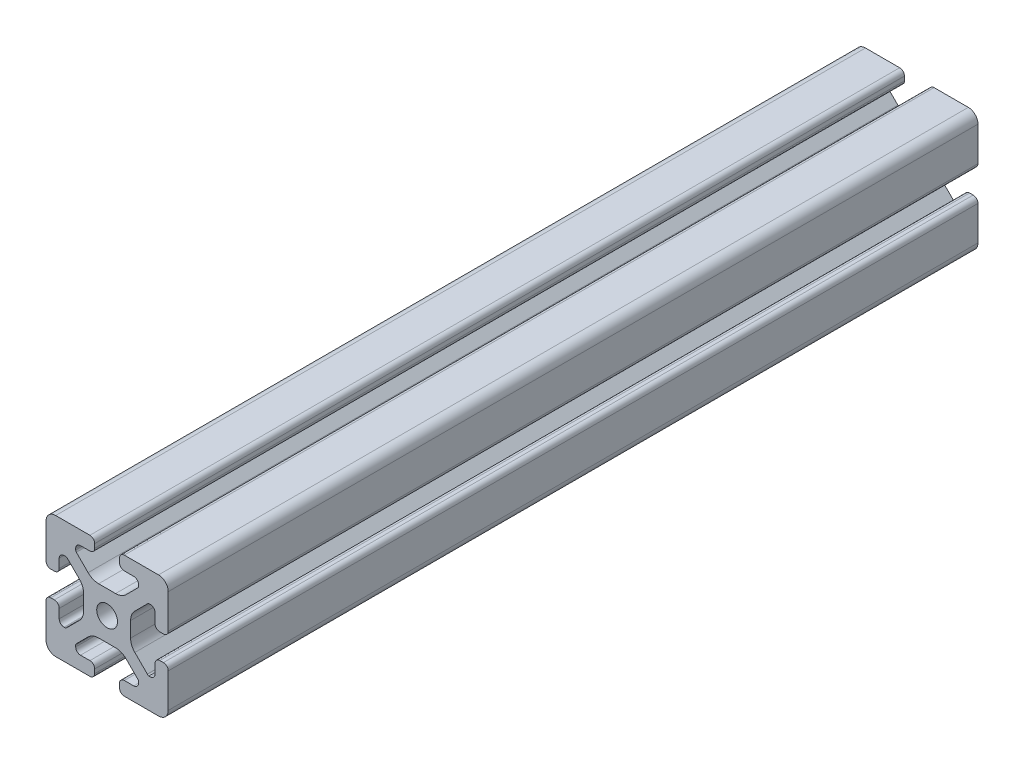
SolidWorks part; units mm, degrees
material "6105-T5 Aluminum"
ref_plane "Front Plane" through (0, 0, 0) normal (0, 0, 1) x (1, 0, 0)
ref_plane "Top Plane" through (0, 0, 0) normal (0, 1, 0) x (1, 0, 0)
ref_plane "Right Plane" through (0, 0, 0) normal (1, 0, 0) x (0, 0, -1)
sketch "Sketch1" plane through (0, 0, 0) normal (0, 0, 1) x (1, 0, 0)
  line L0 (0, 19.7407) -> (0, -19.7407) construction
  line L1 (19.0335, 0) -> (-20.7246, 0) construction
  line L2 (-8.715, -15.5246) -> (-5.63, -15.5246)
  line L3 (-10.285, -13.9546) -> (-10.285, -13.4925)
  line L4 (-6.2171, -9.1098) -> (-10.0624, -12.9551)
  line L5 (2.7773, -7.685) -> (-2.7773, -7.685)
  line L6 (10.0624, -12.9551) -> (6.2171, -9.1098)
  line L7 (10.285, -13.9546) -> (10.285, -13.4925)
  line L8 (5.63, -15.5246) -> (8.715, -15.5246)
  line L9 (4.06, -18.43) -> (4.06, -17.0946)
  line L10 (-4.06, -18.43) -> (-4.06, -17.0946)
  line L11 (15.68, -8.7154) -> (15.68, -5.63)
  line L12 (-14.11, -10.2854) -> (-13.8169, -10.2854)
  line L13 (20, -16.83) -> (20, -5.63)
  line L14 (20, 5.63) -> (20, 13.0011)
  line L15 (-16.83, 20) -> (-5.63, 20)
  line L16 (5.63, 20) -> (12.9796, 20)
  line L18 (-8.715, 15.5246) -> (-5.63, 15.5246)
  line L19 (-20, -17.0184) -> (-20, -5.7579)
  line L20 (-20, 5.573) -> (-20, 13.0045)
  line L21 (-15.68, -8.7154) -> (-15.68, -5.7579)
  line L23 (-16.6746, -20) -> (-5.63, -20)
  line L24 (5.63, -20) -> (13, -20)
  line L53 (14.11, -10.2854) -> (13.6201, -10.2854)
  line L54 (13.1637, -9.947) -> (9.0762, -5.8595)
  line L55 (7.685, -2.5008) -> (7.685, 2.5008)
  line L56 (9.0762, 5.8595) -> (13.2795, 10.0628)
  line L57 (13.8169, 10.2854) -> (14.11, 10.2854)
  line L58 (15.68, 8.7154) -> (15.68, 5.63)
  line L59 (17.25, 4.06) -> (18.43, 4.06)
  line L61 (20, 13.0011) -> (20, 16.83)
  line L62 (16.83, 20) -> (12.9796, 20)
  line L64 (4.06, 18.43) -> (4.06, 17.0946)
  line L65 (5.63, 15.5246) -> (8.715, 15.5246)
  line L66 (10.285, 13.9546) -> (10.285, 13.4925)
  line L67 (10.0624, 12.9551) -> (6.2171, 9.1098)
  line L68 (2.7773, 7.685) -> (-2.7773, 7.685)
  line L69 (-6.2171, 9.1098) -> (-10.0624, 12.9551)
  line L70 (-10.285, 13.4925) -> (-10.285, 13.9546)
  line L72 (-4.06, 17.0946) -> (-4.06, 18.43)
  line L75 (-20, 16.83) -> (-20, 13.0045)
  line L77 (-18.43, 4.003) -> (-17.25, 4.003)
  line L78 (-15.68, 5.573) -> (-15.68, 8.4757)
  line L79 (-14.0552, 10.0447) -> (-13.7199, 10.033)
  line L80 (-13.0405, 9.8238) -> (-9.0762, 5.8595)
  line L81 (-7.685, 2.5008) -> (-7.685, -2.5008)
  line L82 (-9.0762, -5.8595) -> (-13.2795, -10.0628)
  line L85 (-17.25, -4.1204) -> (-18.43, -4.1204)
  line L100 (13, -20) -> (16.83, -20)
  line L103 (18.43, -4.06) -> (17.25, -4.06)
  arc A0 (-5.63, -15.5246) -> (-4.06, -17.0946) centre (-5.63, -17.0946) cw
  arc A1 (-8.715, -15.5246) -> (-10.285, -13.9546) centre (-8.715, -13.9546) cw
  arc A2 (-10.285, -13.4925) -> (-10.0624, -12.9551) centre (-9.525, -13.4925) cw
  arc A3 (-6.2171, -9.1098) -> (-2.7773, -7.685) centre (-2.7773, -12.5496) cw
  arc A4 (2.7773, -7.685) -> (6.2171, -9.1098) centre (2.7773, -12.5496) cw
  arc A5 (10.0624, -12.9551) -> (10.285, -13.4925) centre (9.525, -13.4925) cw
  arc A6 (10.285, -13.9546) -> (8.715, -15.5246) centre (8.715, -13.9546) cw
  arc A7 (4.06, -17.0946) -> (5.63, -15.5246) centre (5.63, -17.0946) cw
  arc A8 (5.63, -20) -> (4.06, -18.43) centre (5.63, -18.43) cw
  arc A9 (-4.06, -18.43) -> (-5.63, -20) centre (-5.63, -18.43) cw
  circle A45 centre (0, 0) radius 3.4
  arc A46 (17.25, -4.06) -> (15.68, -5.63) centre (17.25, -5.63) ccw
  arc A47 (14.11, -10.2854) -> (15.68, -8.7154) centre (14.11, -8.7154) ccw
  arc A48 (13.1637, -9.947) -> (13.6201, -10.2854) centre (13.8117, -9.55) ccw
  arc A49 (7.685, -2.5008) -> (9.0762, -5.8595) centre (12.435, -2.5008) ccw
  arc A50 (9.0762, 5.8595) -> (7.685, 2.5008) centre (12.435, 2.5008) ccw
  arc A51 (13.8169, 10.2854) -> (13.2795, 10.0628) centre (13.8169, 9.5254) ccw
  arc A52 (15.68, 8.7154) -> (14.11, 10.2854) centre (14.11, 8.7154) ccw
  arc A53 (15.68, 5.63) -> (17.25, 4.06) centre (17.25, 5.63) ccw
  arc A54 (18.43, 4.06) -> (20, 5.63) centre (18.43, 5.63) ccw
  arc A55 (20, 16.83) -> (16.83, 20) centre (16.83, 16.83) ccw
  arc A56 (5.63, 20) -> (4.06, 18.43) centre (5.63, 18.43) ccw
  arc A57 (4.06, 17.0946) -> (5.63, 15.5246) centre (5.63, 17.0946) ccw
  arc A58 (10.285, 13.9546) -> (8.715, 15.5246) centre (8.715, 13.9546) ccw
  arc A59 (10.0624, 12.9551) -> (10.285, 13.4925) centre (9.525, 13.4925) ccw
  arc A60 (2.7773, 7.685) -> (6.2171, 9.1098) centre (2.7773, 12.5496) ccw
  arc A61 (-6.2171, 9.1098) -> (-2.7773, 7.685) centre (-2.7773, 12.5496) ccw
  arc A62 (-10.285, 13.4925) -> (-10.0624, 12.9551) centre (-9.525, 13.4925) ccw
  arc A63 (-8.715, 15.5246) -> (-10.285, 13.9546) centre (-8.715, 13.9546) ccw
  arc A64 (-5.63, 15.5246) -> (-4.06, 17.0946) centre (-5.63, 17.0946) ccw
  arc A65 (-4.06, 18.43) -> (-5.63, 20) centre (-5.63, 18.43) ccw
  arc A66 (-16.83, 20) -> (-20, 16.83) centre (-16.83, 16.83) ccw
  arc A67 (-20, 5.573) -> (-18.43, 4.003) centre (-18.43, 5.573) ccw
  arc A68 (-17.25, 4.003) -> (-15.68, 5.573) centre (-17.25, 5.573) ccw
  arc A69 (-14.0552, 10.0447) -> (-15.68, 8.4757) centre (-14.11, 8.4757) ccw
  arc A70 (-13.0405, 9.8238) -> (-13.7199, 10.033) centre (-13.5779, 9.2864) ccw
  arc A71 (-7.685, 2.5008) -> (-9.0762, 5.8595) centre (-12.435, 2.5008) ccw
  arc A72 (-9.0762, -5.8595) -> (-7.685, -2.5008) centre (-12.435, -2.5008) ccw
  arc A73 (-13.8169, -10.2854) -> (-13.2795, -10.0628) centre (-13.8169, -9.5254) ccw
  arc A74 (-15.68, -8.7154) -> (-14.11, -10.2854) centre (-14.11, -8.7154) ccw
  arc A75 (-15.68, -5.7579) -> (-17.25, -4.1204) centre (-17.2485, -5.6904) ccw
  arc A76 (-18.43, -4.1204) -> (-20, -5.7579) centre (-18.4315, -5.6904) ccw
  arc A77 (-20, -17.0184) -> (-16.6746, -20) centre (-16.8354, -16.8341) ccw
  arc A88 (16.83, -20) -> (20, -16.83) centre (16.83, -16.83) ccw
  arc A89 (20, -5.63) -> (18.43, -4.06) centre (18.43, -5.63) ccw
  dimension "D2" = 6.8
  dimension "D7" = 20.57
  dimension "D1" = 40
  dimension "D3" = 4.32
  dimension "D4" = 15.37
  dimension "D5" = 20
  dimension "D6" = 4.32
  dimension "D9" = 15.37
extrude "Extrude1" add sketch "Sketch1" against normal blind 265
